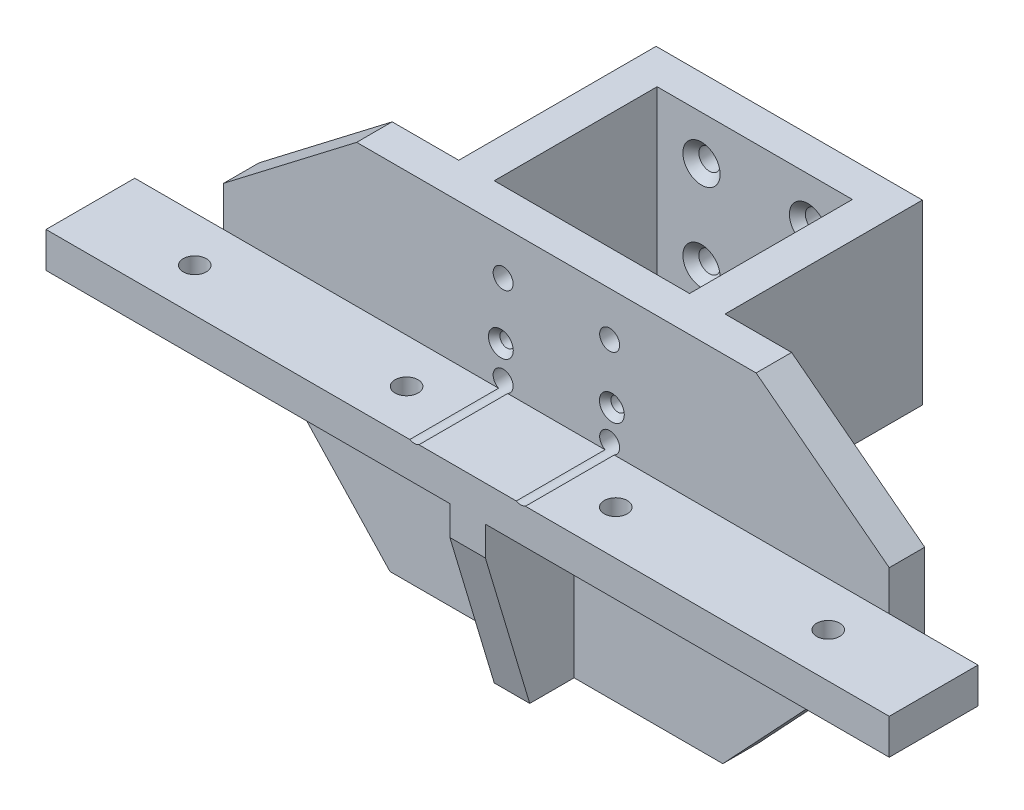
SolidWorks part; units mm, degrees
ref_plane "前视基准面" through (0, 0, 0) normal (0, 0, 1) x (1, 0, 0)
ref_plane "上视基准面" through (0, 0, 0) normal (0, 1, 0) x (1, 0, 0)
ref_plane "右视基准面" through (0, 0, 0) normal (1, 0, 0) x (0, 0, -1)
sketch "草图1" plane through (0, 0, 0) normal (0, 0, 1) x (1, 0, 0)
  line L1 (-31.0656, 46.7213) -> (58.9344, 46.7213)
  line L2 (-61.0656, 23.7213) -> (-61.0656, 6.7213)
  line L3 (-23.5656, -33.2787) -> (51.4344, -33.2787)
  line L4 (88.9344, 23.7213) -> (88.9344, 6.7213)
  line L10 (-31.0656, 46.7213) -> (-61.0656, 23.7213)
  line L11 (58.9344, 46.7213) -> (88.9344, 23.7213)
  line L14 (-61.0656, 6.7213) -> (-23.5656, -33.2787)
  line L15 (51.4344, -33.2787) -> (88.9344, 6.7213)
  line L16 (-23.5656, -33.2787) -> (51.4344, -33.2787)
extrude "凸台-拉伸1" add sketch "草图1" along normal blind 8 contours L3 L15 L4 L11 L1 L10 L2 L14
sketch "草图2" plane through (0, 0, 8) normal (0, 0, 1) x (1, 0, 0)
  line L0 (-61.0656, 6.7213) -> (88.9344, 6.7213)
  line L1 (-80.4124, 14.7213) -> (122.3503, 14.7213)
  line L2 (-61.0656, 14.7213) -> (-61.0656, 6.7213)
  line L3 (-61.0656, 23.7213) -> (-61.0656, 6.7213) construction
  line L4 (88.9344, 6.7213) -> (88.9344, 14.7213)
  line L5 (88.9344, 23.7213) -> (88.9344, 6.7213) construction
  line L6 (88.9344, 14.7213) -> (-61.0656, 14.7213)
  line M5 (88.9344, 6.7213) -> (88.9344, 23.7213)
  line M9 (-61.0656, 23.7213) -> (-61.0656, 6.7213)
  dimension "D1" = 8
extrude "凸台-拉伸2" add sketch "草图2" along normal blind 20 contours L1 L0 M9 M5
sketch "草图3" plane through (88.9344, 0, 0) normal (1, 0, 0) x (0, 0, -1)
  line L0 (-8, 14.7213) -> (-8, 6.7213)
  line L8 (0, 6.7213) -> (0, 23.7213)
  line L9 (0, 23.7213) -> (-8, 23.7213)
  line L10 (-8, 23.7213) -> (-8, 14.7213)
  line L11 (-8, 14.7213) -> (-28, 14.7213)
  line L12 (-28, 14.7213) -> (-28, 6.7213)
  line L13 (-28, 6.7213) -> (-8, 6.7213)
  line L14 (-8, 6.7213) -> (0, 6.7213)
  line L18 (-8, 14.7213) -> (-28, 14.7213)
  line L19 (-28, 14.7213) -> (-28, 6.7213)
  line L20 (-28, 6.7213) -> (-8, 6.7213)
  dimension "D1" = 0
extrude "凸台-拉伸3" add sketch "草图3" along normal blind 20
sketch "草图4" plane through (-61.0656, 0, 0) normal (-1, 0, 0) x (0, 0, 1)
  line L0 (8, 14.7213) -> (8, 6.7213)
  line L1 (8, 14.7213) -> (28, 14.7213)
  line L2 (28, 14.7213) -> (28, 6.7213) construction
  line L3 (28, 14.7213) -> (28, 6.7213)
  line L4 (28, 6.7213) -> (8, 6.7213)
  line L8 (0, 23.7213) -> (0, 6.7213)
  line L9 (0, 6.7213) -> (8, 6.7213)
  line L10 (8, 6.7213) -> (28, 6.7213)
  line L11 (28, 6.7213) -> (28, 14.7213)
  line L12 (28, 14.7213) -> (8, 14.7213)
  line L13 (8, 14.7213) -> (8, 23.7213)
  line L14 (8, 23.7213) -> (0, 23.7213)
  line L15 (0, 23.7213) -> (0, 6.7213)
  line L16 (0, 6.7213) -> (8, 6.7213)
  line L20 (8, 14.7213) -> (8, 23.7213)
  line L21 (8, 23.7213) -> (0, 23.7213)
  line M10 (8, 6.7213) -> (28, 6.7213)
  line M11 (28, 6.7213) -> (28, 14.7213)
  line M12 (28, 14.7213) -> (8, 14.7213)
  dimension "D1" = 0
extrude "凸台-拉伸4" add sketch "草图4" along normal blind 20 contours L0 M12 M10 M11
sketch "草图5" plane through (0, 0, 8) normal (0, 0, 1) x (1, 0, 0)
  line L0 (9.9344, 6.7213) -> (17.9344, 6.7213)
  line L3 (17.9344, 23.3236) -> (17.9344, -48.0404)
  line L4 (9.9344, 21.2896) -> (9.9344, -51.6264)
  line L5 (-61.0656, 6.7213) -> (88.9344, 6.7213) construction
  line L6 (17.9344, 6.7213) -> (17.9344, -33.2973)
  line L7 (17.9344, -33.2973) -> (9.9344, -33.2973)
  line L8 (9.9344, -33.2973) -> (9.9344, 6.7213)
  line M4 (88.9344, 6.7213) -> (-61.0656, 6.7213)
  line M6 (-23.5656, -33.2787) -> (51.4344, -33.2787)
extrude "凸台-拉伸5" add sketch "草图5" along normal blind 20 contours L4 L3 M4 M6
sketch "草图6" plane through (17.9344, 0, 0) normal (1, 0, 0) x (0, 0, -1)
  line L0 (-5.83, 0.1113) -> (-36.5731, 0.1113)
  line L1 (-28, 6.7213) -> (-8, 6.7213) construction
  line L2 (-28, 0.1113) -> (-18, -33.2787)
  line L3 (-28, 6.7213) -> (-28, -33.2787) construction
  line L4 (-28, -33.2787) -> (-8, -33.2787) construction
  line L5 (-18, -33.2787) -> (-28, -33.2787)
  line L6 (-28, -33.2787) -> (-28, 0.1113)
  line M4 (-28, 6.7213) -> (-28, -33.2787)
  line M5 (-28, -33.2787) -> (-8, -33.2787)
  dimension "D1" = 6.61
extrude "切除-拉伸1" cut sketch "草图6" against normal blind 20 contours L2 M4 M5
sketch "草图7" plane through (0, 46.7213, 0) normal (0, 1, 0) x (1, 0, 0)
  line L3 (35.9344, 36.2) -> (35.9344, 0)
  line L4 (-16.0656, 45.15) -> (-16.0656, 0)
  line L5 (43.9344, 45.15) -> (43.9344, 0)
  line L7 (-31.0656, 0) -> (58.9344, 0) construction
  line L8 (-16.0656, 45.15) -> (43.9344, 45.15)
  line L9 (-8.0656, 36.2) -> (35.9344, 36.2)
  line L10 (-8.0656, 36.2) -> (-8.0656, 0)
  line L12 (-8.0656, 0) -> (-8.0656, 36.2)
  line L13 (35.9344, 36.2) -> (35.9344, 0)
  line L14 (35.9344, 0) -> (43.9344, 0)
  line L15 (43.9344, 0) -> (43.9344, 45.15)
  line L16 (43.9344, 45.15) -> (-16.0656, 45.15)
  line L17 (-16.0656, 45.15) -> (-16.0656, 0)
  line L18 (-16.0656, 0) -> (-8.0656, 0)
  line M8 (58.9344, 0) -> (-31.0656, 0)
  dimension "D4" = 8
extrude "凸台-拉伸6" add sketch "草图7" against normal blind 40 contours L10 L9 L3 L5 L8 L4 M8
sketch "草图9" plane through (0, 0, 8) normal (0, 0, 1) x (1, 0, 0)
  line L0 (-61.0656, 23.7213) -> (88.9344, 23.7213)
  line L1 (-68.2563, -1.2787) -> (98.3912, -1.2787)
  line L2 (13.9344, 50.7558) -> (13.9344, -40.6595)
  line L3 (1.4344, 53.665) -> (1.4344, -43.7519)
  line L4 (26.4344, 52.2487) -> (26.4344, -42.6888)
  dimension "D1" = 25
  dimension "D2" = 12.5
  dimension "D3" = 12.5
hole_wizard "孔2" positions "3D草图3" profile "草图12" legacy end condition up to next
sketch3d "3D草图3"
  line L0 (-61.0656, 23.7213, 8) -> (88.9344, 23.7213, 8) construction
  line L1 (26.4344, 52.2487, 8) -> (26.4344, -42.6888, 8) construction
  line L2 (-68.2563, -1.2787, 8) -> (98.3912, -1.2787, 8) construction
  line L3 (1.4344, 53.665, 8) -> (1.4344, -43.7519, 8) construction
  point P0 (1.4208, 23.7213, 8)
  point P4 (26.4344, 23.7213, 8)
  point P8 (26.4344, -1.2787, 8)
  point P12 (1.4344, -1.2787, 8)
sketch "草图12" plane through (1.4208, 23.7213, 8) normal (1, 0, 0) x (0, -1, 0)
  line L0 (0, 0) -> (0, 8.9614)
  line L1 (0, 8.9614) -> (1.6, 8)
  line L2 (1.6, 8) -> (1.6, 1.3804)
  line L3 (1.6, 1.3804) -> (2.8, 0)
  line L4 (2.8, 0) -> (0, 0)
  line L5 (0, -14.3089) -> (0, 102.4216) construction
  line L6 (0, 8.9614) -> (-1.6, 8) construction
  line L7 (-1.6, 1.3804) -> (-2.8, 0) construction
  dimension "直径" = 3.2
  dimension "深度" = 8
  dimension "锥坑直径" = 5.6
  dimension "锥坑角度" = 82
  dimension "导头角度" = 118
sketch "草图14" plane through (0, 0, -36.2) normal (0, 0, 1) x (1, 0, 0)
  line L0 (13.9344, 6.7213) -> (13.9344, 46.7213)
  line L1 (-8.0656, 6.7213) -> (35.9344, 6.7213) construction
  line L2 (-8.0656, 46.7213) -> (35.9344, 46.7213) construction
  line L3 (-8.0656, 26.7213) -> (35.9344, 26.7213)
  line L4 (-8.0656, 6.7213) -> (-8.0656, 46.7213) construction
  line L5 (35.9344, 6.7213) -> (35.9344, 46.7213) construction
  line L6 (1.9344, 4.1358) -> (1.9344, 68.7387)
  line L7 (25.9344, 4.1358) -> (25.9344, 75.3272)
  line L8 (-6.2258, 36.7213) -> (31.1866, 36.7213)
  line L9 (-6.2258, 16.7213) -> (31.1866, 16.7213)
  dimension "D1" = 12
  dimension "D2" = 12
  dimension "D3" = 10
  dimension "D4" = 10
hole_wizard "M4 平头机械螺钉的锥形沉头孔1" positions "3D草图6" profile "草图16" countersink size "M4" standard "ANSI Metric"
sketch3d "3D草图6"
  line L0 (1.9344, 4.1358, -36.2) -> (1.9344, 68.7387, -36.2) construction
  line L1 (-6.2258, 16.7213, -36.2) -> (31.1866, 16.7213, -36.2) construction
  line L2 (25.9344, 4.1358, -36.2) -> (25.9344, 75.3272, -36.2) construction
  line L3 (-6.2258, 36.7213, -36.2) -> (31.1866, 36.7213, -36.2) construction
  point P0 (1.9344, 16.7213, -36.2)
  point P6 (25.9344, 16.7213, -36.2)
  point P10 (25.9344, 36.7213, -36.2)
  point P14 (1.9344, 36.7213, -36.2)
sketch "草图16" plane through (1.9344, 16.7213, -36.2) normal (1, 0, 0) x (0, -1, 0)
  line L0 (0, 0) -> (0, 8.95)
  line L1 (0, 8.95) -> (2.4, 8.95)
  line L2 (2.4, 8.95) -> (2.4, 2.3)
  line L3 (2.4, 2.3) -> (4.7, 0)
  line L5 (4.7, 0) -> (0, 0)
  line L6 (-2.4, 2.3) -> (-4.7, 0) construction
  line L11 (0, -6.35) -> (0, 107.95) construction
  dimension "通孔孔直径" = 4.8
  dimension "通孔孔深度" = 8.95
  dimension "近端锥形沉头孔直径" = 9.4
  dimension "近端锥形沉头孔角度" = 90
sketch "草图17" plane through (0, 14.7213, 0) normal (0, 1, 0) x (1, 0, 0)
  circle A0 centre (85.1844, -18) radius 2.6
  circle A1 centre (37.312, -18) radius 2.6
  circle A2 centre (-9.8156, -18) radius 2.6
  circle A3 centre (-57.3156, -18.2359) radius 2.6
  dimension "D7" = 5.2
  dimension "D8" = 5.2
  dimension "D9" = 5.2
  dimension "D10" = 5.2
extrude "切除-拉伸3" cut sketch "草图17" against normal blind 40
sketch "草图22" plane through (0, 0, -45.15) normal (0, 0, -1) x (-1, 0, 0)
  line L0 (-43.9344, 26.7213) -> (16.0656, 26.7213)
  line L1 (-43.9344, 6.7213) -> (-43.9344, 46.7213) construction
  line L2 (16.0656, 6.7213) -> (16.0656, 46.7213) construction
  line L3 (-13.9344, 46.7213) -> (-13.9344, 6.7213)
  line L4 (16.0656, 46.7213) -> (-43.9344, 46.7213) construction
  line L5 (16.0656, 6.7213) -> (-43.9344, 6.7213) construction
  line L6 (-1.9344, 55.4753) -> (-1.9344, 1.1578)
  line L7 (-25.9344, 55.4753) -> (-25.9344, 2.3807)
  line L8 (-46.0684, 36.7213) -> (21.0896, 36.7213)
  line L9 (-46.0684, 16.7213) -> (21.0896, 16.7213)
  circle A0 centre (-25.9344, 36.7213) radius 2.25
  circle A1 centre (-1.9344, 36.7213) radius 2.25
  circle A2 centre (-1.9344, 16.7213) radius 2.25
  circle A3 centre (-25.9344, 16.7213) radius 2.25
  dimension "D5" = 4.5
  dimension "D6" = 4.5
  dimension "D7" = 4.5
  dimension "D8" = 4.5
  dimension "D1" = 10
  dimension "D2" = 10
  dimension "D3" = 12
  dimension "D4" = 12
extrude "切除-拉伸4" cut sketch "草图22" against normal through all contours A1 | A2 | A3 | A0
sketch "草图24" plane through (0, 46.7213, 0) normal (0, 1, 0) x (1, 0, 0)
  line L0 (-26.9392, 44.47) -> (59.6308, 44.47)
  line L1 (-16.0656, 45.15) -> (43.9344, 45.15) construction
  line L2 (-16.0656, 44.47) -> (-16.0656, 45.15)
  line L3 (-16.0656, 45.15) -> (-16.0656, 0) construction
  line L4 (-16.0656, 45.15) -> (43.9344, 45.15)
  line L5 (43.9344, 45.15) -> (43.9344, 44.47)
  line L6 (43.9344, 45.15) -> (43.9344, 0) construction
  line L7 (43.9344, 44.47) -> (-16.0656, 44.47)
  line M11 (43.9344, 0) -> (43.9344, 45.15)
  line M12 (43.9344, 45.15) -> (-16.0656, 45.15)
  line M13 (-16.0656, 45.15) -> (-16.0656, 0)
  dimension "D1" = 0.68
extrude "切除-拉伸5" cut sketch "草图24" against normal blind 40 contours L0 M13 M11 M12
sketch "草图26" plane through (0, 0, -36.2) normal (0, 0, 1) x (1, 0, 0)
  line L4 (35.9344, 46.7213) -> (-8.0656, 46.7213)
  line L5 (-8.0656, 46.7213) -> (-8.0656, 6.7213)
  line L6 (-8.0656, 6.7213) -> (35.9344, 6.7213)
  line L7 (35.9344, 6.7213) -> (35.9344, 46.7213)
  line L8 (35.9344, 46.7213) -> (-8.0656, 46.7213)
  line L9 (-8.0656, 46.7213) -> (-8.0656, 6.7213)
  line L10 (-8.0656, 6.7213) -> (35.9344, 6.7213)
  line L11 (35.9344, 6.7213) -> (35.9344, 46.7213)
  circle A0 centre (1.9344, 16.7213) radius 4.7 construction
  circle A1 centre (1.9344, 36.7213) radius 4.7 construction
  circle A2 centre (25.9344, 16.7213) radius 4.7 construction
  circle A3 centre (25.9344, 36.7213) radius 4.7 construction
  circle A4 centre (1.9344, 16.7213) radius 4.7
  circle A5 centre (1.9344, 36.7213) radius 4.7
  circle A6 centre (25.9344, 16.7213) radius 4.7
  circle A7 centre (25.9344, 36.7213) radius 4.7
  dimension "D1" = 0
sketch "草图27" plane through (0, 0, -36.2) normal (0, 0, 1) x (1, 0, 0)
  line L4 (35.9344, 46.7213) -> (-8.0656, 46.7213)
  line L5 (-8.0656, 46.7213) -> (-8.0656, 6.7213)
  line L6 (-8.0656, 6.7213) -> (35.9344, 6.7213)
  line L7 (35.9344, 6.7213) -> (35.9344, 46.7213)
  line L8 (35.9344, 46.7213) -> (-8.0656, 46.7213)
  line L9 (-8.0656, 46.7213) -> (-8.0656, 6.7213)
  line L10 (-8.0656, 6.7213) -> (35.9344, 6.7213)
  line L11 (35.9344, 6.7213) -> (35.9344, 46.7213)
  circle A0 centre (25.9344, 16.7213) radius 4.7 construction
  circle A1 centre (25.9344, 36.7213) radius 4.7 construction
  circle A2 centre (1.9344, 16.7213) radius 4.7 construction
  circle A3 centre (1.9344, 36.7213) radius 4.7 construction
  circle A4 centre (25.9344, 16.7213) radius 4.7
  circle A5 centre (25.9344, 36.7213) radius 4.7
  circle A6 centre (1.9344, 16.7213) radius 4.7
  circle A7 centre (1.9344, 36.7213) radius 4.7
  dimension "D1" = 0
sketch "草图29" plane through (0, 46.7213, 0) normal (0, 1, 0) x (1, 0, 0)
  line L0 (35.9344, 36.7) -> (-8.0656, 36.7)
  line L3 (35.9344, 36.2) -> (-8.0656, 36.2) construction
  line L4 (35.9344, 36.2) -> (35.9344, 36.7)
  line L5 (-8.0656, 36.2) -> (-8.0656, 36.7)
  line L6 (-8.0656, 36.2) -> (35.9344, 36.2)
  dimension "D1" = 0.5
extrude "切除-拉伸10" cut sketch "草图29" against normal through all
